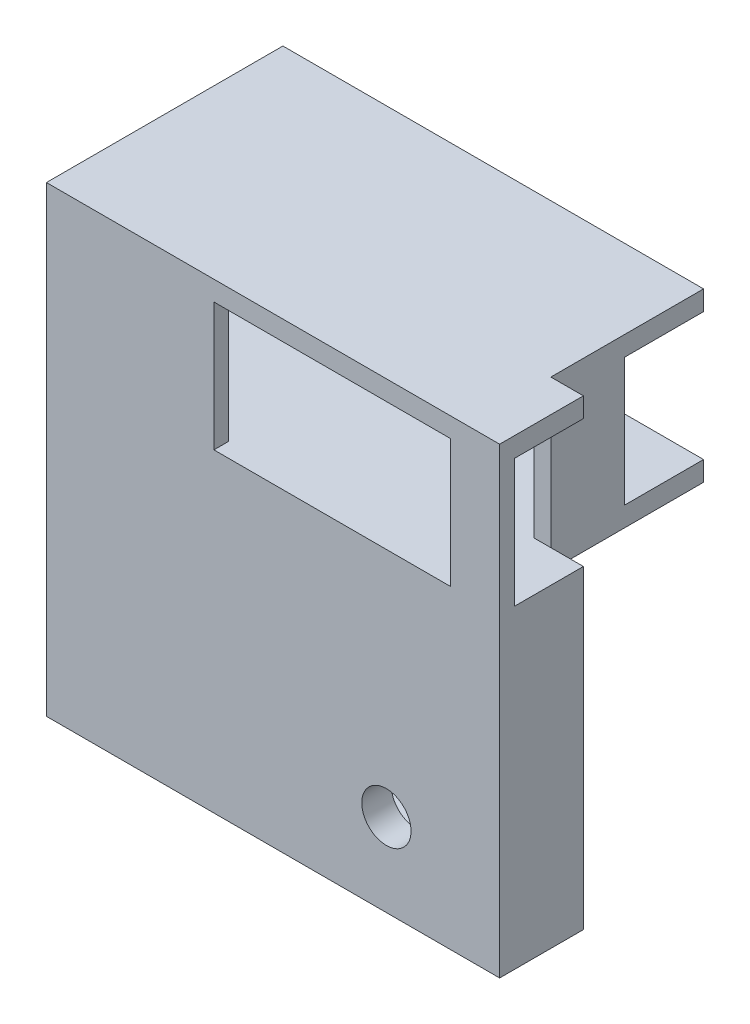
SolidWorks part; units mm, degrees
ref_plane "前视基准面" through (0, 0, 0) normal (0, 0, 1) x (1, 0, 0)
ref_plane "上视基准面" through (0, 0, 0) normal (0, 1, 0) x (1, 0, 0)
ref_plane "右视基准面" through (0, 0, 0) normal (1, 0, 0) x (0, 0, -1)
sketch "草图1" plane through (0, 0, 0) normal (0, 0, 1) x (1, 0, 0)
  line L1 (0, 0) -> (-24, 0)
  line L2 (0, 0) -> (0, 13)
  line L3 (0, 13) -> (-24, 13)
  line L4 (-24, 0) -> (-24, 13)
  line L5 (5, -2) -> (-29, -2)
  line L6 (5, -2) -> (5, 15)
  line L7 (5, 15) -> (-29, 15)
  line L8 (-29, -2) -> (-29, 15)
  dimension "D2" = 17
  dimension "D3" = 13
extrude "凸台-拉伸1" add sketch "草图1" along normal blind 1.5 contours L2 L3 L4 L1 | L6 L7 L8 L5
sketch "草图3" plane through (0, 0, 0) normal (0, 0, -1) x (-1, 0, 0)
  line L5 (29, -2) -> (-5, -2)
  line L6 (29, -2) -> (29, 0)
  line L7 (29, 0) -> (-5, 0)
  line L8 (-5, -2) -> (-5, 0)
  line L9 (29, 13) -> (-5, 13)
  line L10 (29, 13) -> (29, 15)
  line L11 (29, 15) -> (-5, 15)
  line L12 (-5, 13) -> (-5, 15)
sketch "草图4" plane through (0, 0, 0) normal (0, 0, 1) x (1, 0, 0)
  circle A0 centre (2.6, 10) radius 1
  circle A1 centre (2.6, 3) radius 1
  circle A2 centre (-26.6, 10) radius 1
  circle A3 centre (-26.6, 3) radius 1
extrude "凸台-拉伸4" add sketch "草图4" against normal blind 1 draft 43
extrude "凸台-拉伸5" add sketch "草图3" along normal blind 7
sketch "草图5" plane through (0, 0, -7) normal (0, 0, -1) x (-1, 0, 0)
  line L0 (29, 15) -> (-5, 15) construction
  line L1 (-1.6983, 15) -> (0, 15)
  line L2 (-1.6983, 15) -> (-1.6983, -2)
  line L3 (-1.6983, -2) -> (0, -2)
  line L4 (0, 15) -> (0, -2)
  line L5 (-5, -2) -> (29, -2) construction
  line L7 (0, 0) -> (29, 0)
  line L8 (0, 0) -> (0, -2)
  line L9 (0, -2) -> (29, -2)
  line L10 (29, 0) -> (29, -2)
  line L11 (0, 15) -> (29, 15)
  line L12 (0, 15) -> (0, 13)
  line L13 (0, 13) -> (29, 13)
  line L14 (29, 15) -> (29, 13)
  line M1 (29, 0) -> (-5, 0)
  line M3 (-5, -2) -> (29, -2)
  line M4 (29, -2) -> (29, 0)
extrude "凸台-拉伸6" add sketch "草图5" along normal blind 15.5 contours L4 L2 M1 M3 | L4 M1 M3 M4 | L4 L1 L2 M1 | L14 L11 L4 L13
sketch "草图6" plane through (0, 0, 0) normal (-1, 0, 0) x (0, 0, 1)
  line L0 (-22.5, 0) -> (-7, 0) construction
  line L1 (-22.5, 13) -> (-14.5, 13)
  line L2 (-22.5, 13) -> (-22.5, 0)
  line L3 (-22.5, 0) -> (-14.5, 0)
  line L4 (-14.5, 13) -> (-14.5, 0)
extrude "切除-拉伸1" cut sketch "草图6" against normal up to next
sketch "草图8" plane through (0, 0, 1.5) normal (0, 0, 1) x (1, 0, 0)
  line L1 (5, 15) -> (-41, 15)
  line L2 (5, 15) -> (5, -76)
  line L3 (5, -76) -> (-41, -76)
  line L4 (-41, 15) -> (-41, -76)
sketch "草图9" plane through (-29, 0, 0) normal (-1, 0, 0) x (0, 0, 1)
  line L0 (-22.5, 15) -> (1.5, 15)
  line L1 (1.5, 15) -> (1.5, -2)
  line L2 (1.5, -2) -> (-22.5, -2)
  line L3 (-22.5, -2) -> (-22.5, 0)
  line L4 (-22.5, 0) -> (0, 0)
  line L5 (0, 0) -> (0, 13)
  line L6 (0, 13) -> (-22.5, 13)
  line L7 (-22.5, 13) -> (-22.5, 15)
extrude "凸台-拉伸7" add sketch "草图9" along normal up to vertex (12 mm away) up to point (-41, 15, 1.5)
sketch "草图10" plane through (-41, 0, 0) normal (-1, 0, 0) x (0, 0, 1)
  line L1 (1.5, 15) -> (-22.5, 15)
  line L2 (1.5, 15) -> (1.5, -2)
  line L3 (1.5, -2) -> (-22.5, -2)
  line L4 (-22.5, 15) -> (-22.5, -2)
  line L5 (1.5, -2) -> (-22.5, -2)
  line L6 (1.5, -2) -> (1.5, -31.9236)
  line L7 (1.5, -31.9236) -> (-22.5, -31.9236)
  line L8 (-22.5, -2) -> (-22.5, -31.9236)
  line M9 (-22.5, 15) -> (-22.5, 13)
  line M10 (-22.5, 13) -> (0, 13)
  line M11 (0, 13) -> (0, 0)
  line M12 (0, 0) -> (-22.5, 0)
  line M13 (-22.5, 0) -> (-22.5, -2)
  line M14 (-22.5, -2) -> (1.5, -2)
  line M15 (1.5, -2) -> (1.5, 15)
  line M16 (1.5, 15) -> (-22.5, 15)
extrude "凸台-拉伸8" add sketch "草图10" against normal blind 3 contours L8 L7 L6 M14 | L4 M10 M12 M11 | M16 M9 M10 M11 M12 M13 M14 M15
sketch "草图11" plane through (0, 0, 1.5) normal (0, 0, 1) x (1, 0, 0)
  line L1 (-41, -31.9236) -> (5, -31.9236)
  line L2 (-41, -31.9236) -> (-41, -2)
  line L3 (-41, -2) -> (5, -2)
  line L4 (5, -31.9236) -> (5, -2)
extrude "凸台-拉伸9" add sketch "草图11" against normal blind 3
sketch "草图12" plane through (0, 0, -1.5) normal (0, 0, -1) x (-1, 0, 0)
  line L0 (-5, -2) -> (38, -2) construction
  line L1 (-5, -31.9236) -> (16.5, -31.9236)
  line L2 (-5, -31.9236) -> (-5, -2)
  line L3 (-5, -2) -> (16.5, -2)
  line L4 (16.5, -31.9236) -> (16.5, -2)
  line L5 (38, -2) -> (38, -31.9236) construction
  line L6 (-2.72, -28.8426) -> (14.0297, -28.8426)
  line L7 (-2.72, -28.8426) -> (-2.72, -4.1587)
  line L8 (-2.72, -4.1587) -> (14.0297, -4.1587)
  line L9 (14.0297, -28.8426) -> (14.0297, -4.1587)
  line L10 (16.5, -28.721) -> (38, -28.721)
  line L11 (16.5, -28.721) -> (16.5, -31.9236)
  line L12 (16.5, -31.9236) -> (38, -31.9236)
  line L13 (38, -28.721) -> (38, -31.9236)
  line L14 (16.5, -2) -> (38, -2)
  line L15 (16.5, -2) -> (16.5, -4.1587)
  line L16 (16.5, -4.1587) -> (38, -4.1587)
  line L17 (38, -2) -> (38, -4.1587)
  line L19 (35.6503, -28.721) -> (38, -28.721)
  line L20 (35.6503, -28.721) -> (35.6503, -4.1587)
  line L21 (35.6503, -4.1587) -> (38, -4.1587)
  line L22 (38, -28.721) -> (38, -4.1587)
  line M1 (38, -31.9236) -> (38, -2)
  line M2 (38, -2) -> (-5, -2)
  line M3 (-5, -2) -> (-5, -31.9236)
  line M4 (-5, -31.9236) -> (38, -31.9236)
extrude "凸台-拉伸10" add sketch "草图12" along normal up to vertex contours L4 L9 L6 L7 L8 M4 M2 M3 | L10 L4 M4 M1 | L20 L10 L16 M1 | L4 L16 M1 M2
sketch "草图13" plane through (0, -31.9236, 0) normal (0, -1, 0) x (1, 0, 0)
  line L0 (-38, -22.5) -> (-22.5, -7)
  line L1 (5, -7) -> (-38, -7) construction
  line L2 (-22.5, -7) -> (-38, -7)
  line L3 (-38, -7) -> (-38, -22.5)
extrude "凸台-拉伸11" add sketch "草图13" against normal up to vertex
sketch "草图14" plane through (0, 0, 1.5) normal (0, 0, 1) x (1, 0, 0)
  circle A0 centre (-6.4936, -23.5227) radius 2.5
  dimension "D3" = 5
extrude "切除-拉伸2" cut sketch "草图14" against normal up to next contours A0
